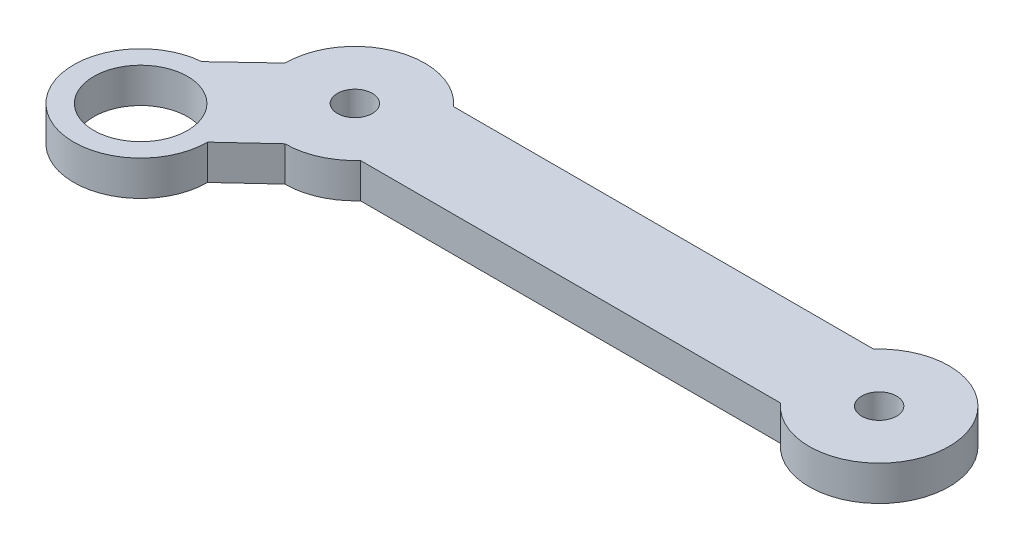
SolidWorks part; units mm, degrees
ref_plane "Plan de face" through (0, 0, 0) normal (0, 0, 1) x (1, 0, 0)
ref_plane "Plan de dessus" through (0, 0, 0) normal (0, 1, 0) x (1, 0, 0)
ref_plane "Plan de droite" through (0, 0, 0) normal (1, 0, 0) x (0, 0, -1)
sketch "Esquisse10" plane through (0, 0, 0) normal (0, 1, 0) x (1, 0, 0)
  line L0 (0, 0) -> (-45, 0) construction
  line L1 (-40.5279, -4) -> (-4.4721, -4)
  line L2 (-40.5279, 4) -> (-4.4721, 4)
  line L3 (-45, 0) -> (-54.1924, -9.1924) construction
  line L4 (-45, 0) -> (-54.1924, -9.1924)
  line L5 (-54.6776, -3.4629) -> (-51, 0)
  line L6 (-48.4424, -9.1924) -> (-45, -6)
  circle A0 centre (0, 0) radius 1.5
  circle A1 centre (0, 0) radius 6
  circle A2 centre (-216.2188, -44.0834) radius 1.0496
  circle A3 centre (-45, 0) radius 1.5
  circle A4 centre (-45, 0) radius 6
  circle A5 centre (-54.1924, -9.1924) radius 4.024
  circle A6 centre (-54.1924, -9.1924) radius 5.75
  dimension "D1" = 3
  dimension "D2" = 12
  dimension "D4" = 3
  dimension "D5" = 12
  dimension "D10" = 11.5
  dimension "D11" = 13
  dimension "D9" = 8.048
  dimension "D12" = 5.0514
  dimension "D3" = 45
  dimension "D6" = 4
  dimension "D7" = 4
  dimension "D8" = 135
extrude "Boss.-Extru.1" add sketch "Esquisse10" along normal blind 3
